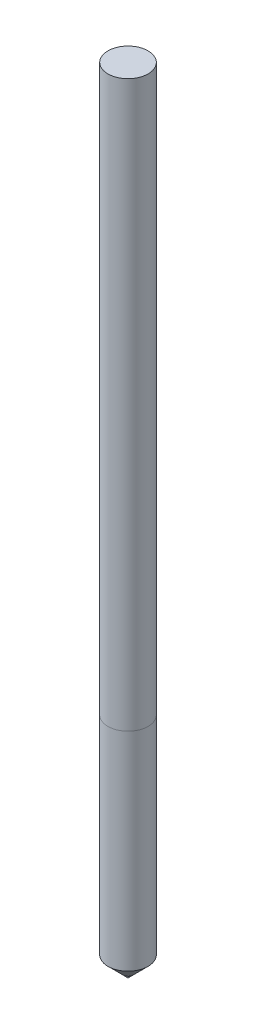
SolidWorks part; units mm, degrees
ref_plane "Front Plane" through (0, 0, 0) normal (0, 0, 1) x (1, 0, 0)
ref_plane "Top Plane" through (0, 0, 0) normal (0, 1, 0) x (1, 0, 0)
ref_plane "Right Plane" through (0, 0, 0) normal (1, 0, 0) x (0, 0, -1)
sketch "Sketch1" plane through (0, 0, 0) normal (0, 0, 1) x (1, 0, 0)
  line L0 (-8.5831, -33.6137) -> (11.4169, -33.6137) construction
  line L1 (-2.0831, -69.909) -> (1.4169, -69.909)
  line L2 (1.4169, -73.4137) -> (-2.0831, -69.909)
  line L3 (1.4169, 65.091) -> (1.4169, -33.6137)
  line L4 (-2.0831, -69.909) -> (-2.0831, 65.091)
  line L6 (1.4169, 65.091) -> (-2.0831, 65.091)
  line L7 (-8.5831, -33.6137) -> (-8.5831, -23.6137) construction
  line L8 (-8.5831, -23.6137) -> (11.4169, -23.6137) construction
  line L9 (11.4169, -23.6137) -> (11.4169, -33.6137) construction
  line L10 (-8.5831, -0.6137) -> (11.4169, -0.6137) construction
  line L11 (11.4169, -0.6137) -> (11.4169, 9.3863) construction
  line L12 (11.4169, 9.3863) -> (-8.5831, 9.3863) construction
  line L13 (-8.5831, 9.3863) -> (-8.5831, -0.6137) construction
  line L14 (1.4169, -73.4137) -> (1.4169, -33.6137)
  dimension "D1" = 10
  dimension "D2" = 10
revolve "Revolve1" add sketch "Sketch1" angle 360 about L14
ref_plane "Plane2" through (4.9169, 0, 0) normal (1, 0, 0) x (0, 0, -1)
sketch "Sketch4" plane through (4.9169, 0, 0) normal (1, 0, 0) x (0, 0, -1)
  line L0 (0, -33.6137) -> (0, -80.1014)
  line L1 (-9.2309, -33.6137) -> (11.0652, -33.6137)
split line "Split Line2"
